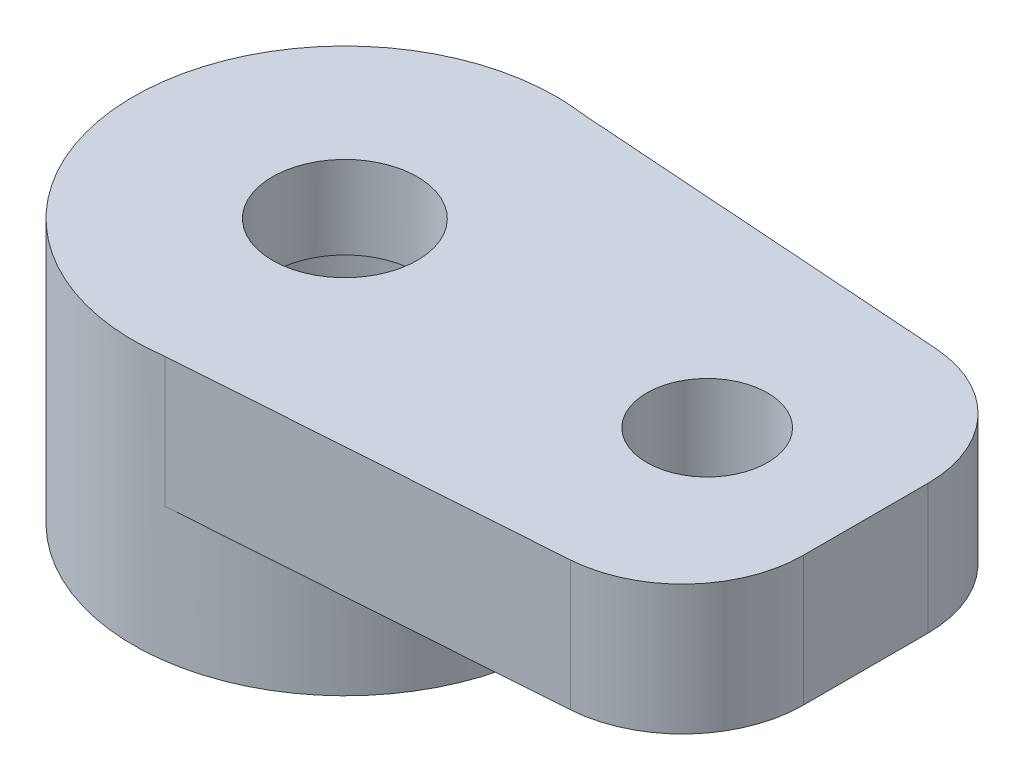
SolidWorks part; units mm, degrees
ref_plane "Alzado" through (0, 0, 0) normal (0, 0, 1) x (1, 0, 0)
ref_plane "Planta" through (0, 0, 0) normal (0, 1, 0) x (1, 0, 0)
ref_plane "Vista lateral" through (0, 0, 0) normal (1, 0, 0) x (0, 0, -1)
sketch "Croquis1" plane through (0, 0, 0) normal (0, 1, 0) x (1, 0, 0)
  line L0 (0, 0) -> (21.5, 0) construction
  line L1 (0.486, 3.4661) -> (21.5, 2)
  line L2 (0.486, -3.4661) -> (21.5, -2)
  arc A0 (0.486, 3.4661) -> (0.486, -3.4661) centre (0, 0) ccw
  arc A1 (21.5, -2) -> (21.5, 2) centre (21.5, 0) ccw
  dimension "D1" = 7
  dimension "D2" = 4
  dimension "D3" = 21.5
extrude "Saliente-Extruir1" add sketch "Croquis1" along normal blind 2.15
sketch "Croquis2" plane through (0, 0, 0) normal (0, -1, 0) x (1, 0, 0)
  circle A0 centre (0, 0) radius 3.5
extrude "Saliente-Extruir2" add sketch "Croquis2" along normal blind 2.22 contours A0
sketch "Croquis3" plane through (0, 2.15, 0) normal (0, 1, 0) x (1, 0, 0)
  circle A0 centre (0, 0) radius 1.2
  dimension "D1" = 2.4
extrude "Cortar-Extruir1" cut sketch "Croquis3" against normal blind 7.22 contours A0
sketch "Croquis4" plane through (0, -2.22, 0) normal (0, -1, 0) x (1, 0, 0)
  circle A0 centre (0, 0) radius 2.175
  dimension "D1" = 4.35
extrude "Cortar-Extruir2" cut sketch "Croquis4" against normal blind 3 contours A0
sketch "Croquis5" plane through (0, 2.15, 0) normal (0, 1, 0) x (1, 0, 0)
  circle A0 centre (21.5, 0) radius 1
  circle A1 centre (15.5, 0) radius 1
  circle A2 centre (6, 0) radius 1
  circle A3 centre (0, 0) radius 1.2 construction
  dimension "D1" = 2
  dimension "D2" = 6
  dimension "D3" = 2
  dimension "D4" = 2
  dimension "D6" = 6
extrude "Cortar-Extruir3" cut sketch "Croquis5" against normal blind 10
sketch "Sketch1" plane through (0, 2.15, 0) normal (0, 1, 0) x (1, 0, 0)
  line L0 (21.5, 2) -> (8.6249, 2.8983)
  line L1 (21.5, 2) -> (0.486, 3.4661) construction
  line L2 (8.6249, 2.8983) -> (8.6249, -2.8983)
  line L3 (0.486, -3.4661) -> (21.5, -2) construction
  line L4 (8.6249, -2.8983) -> (21.5, -2)
  arc A0 (21.5, 2) -> (21.5, -2) centre (21.5, 0) cw
extrude "Cut-Extrude1" cut sketch "Sketch1" against normal blind 10
fillet "Fillet1" radius 2 2 edges at (8.6249, 1.075, 2.8983) (8.6249, 1.075, -2.8983)
